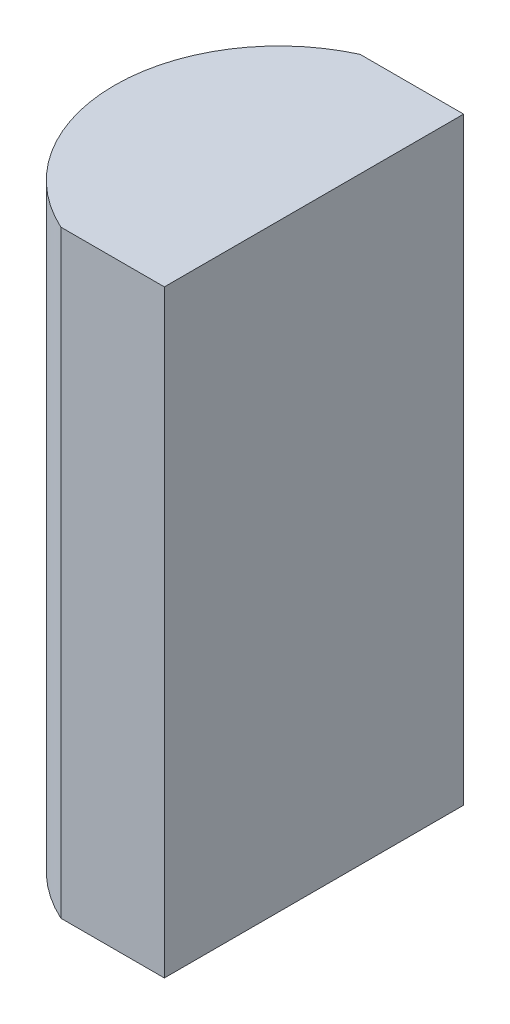
SolidWorks part; units mm, degrees
ref_plane "前视基准面" through (0, 0, 0) normal (0, 0, 1) x (1, 0, 0)
ref_plane "上视基准面" through (0, 0, 0) normal (0, 1, 0) x (1, 0, 0)
ref_plane "右视基准面" through (0, 0, 0) normal (1, 0, 0) x (0, 0, -1)
sketch "草图1" plane through (0, 0, 0) normal (0, 1, 0) x (1, 0, 0)
  line L0 (10.7432, 0) -> (-9.7696, 0) construction
  line L1 (2.9804, 3) -> (5.0552, 3)
  line L2 (2.9804, -3) -> (5.0552, -3)
  line L3 (5.0552, 3) -> (5.0552, -3)
  arc A0 (2.9804, 3) -> (2.9804, -3) centre (4.3552, 0) ccw
  point P19 (1.0552, 0)
  point P20 (5.0552, 0)
  dimension "D2" = 3
  dimension "D3" = 3.3
  dimension "D4" = 4
  dimension "D1" = 3
extrude "凸台-拉伸1" add sketch "草图1" along normal blind 12
